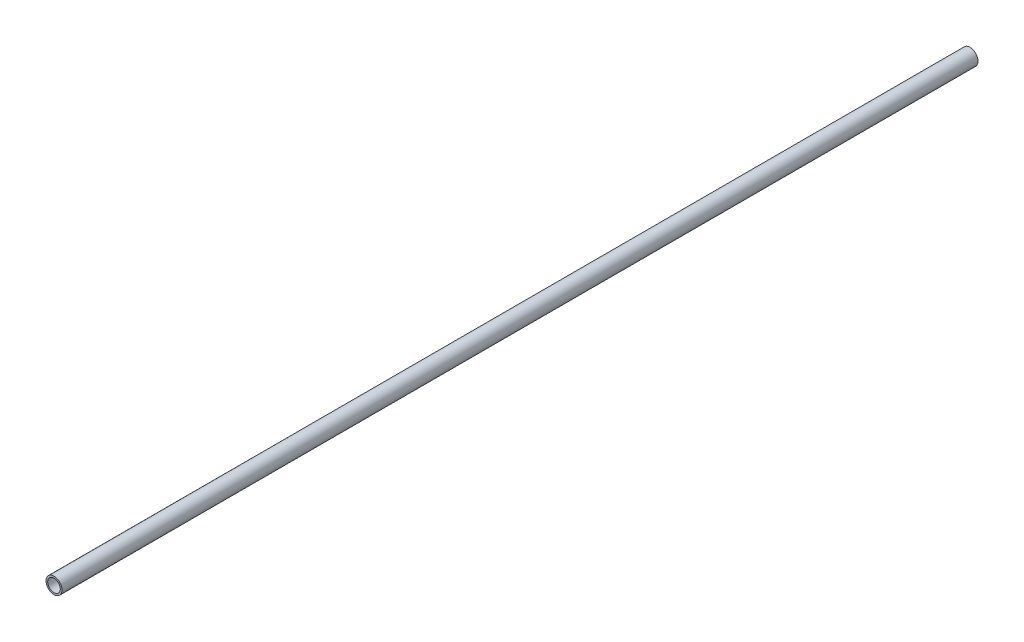
SolidWorks part; units mm, degrees
material "PVC 0.007 Plasticized"
ref_plane "Front Plane" through (0, 0, 0) normal (0, 0, 1) x (1, 0, 0)
ref_plane "Top Plane" through (0, 0, 0) normal (0, 1, 0) x (1, 0, 0)
ref_plane "Right Plane" through (0, 0, 0) normal (1, 0, 0) x (0, 0, -1)
sketch "Sketch1" plane through (0, 0, 0) normal (0, 0, 1) x (1, 0, 0)
  line L0 (10.4648, 0) -> (13.335, 0) construction
  circle A0 centre (0, 0) radius 13.335 construction
  circle A1 centre (0, 0) radius 10.4648 construction
  dimension "ID" = 20.9296
  dimension "OD" = 26.67
  dimension "Wall Thickness" = 2.8702
sketch "Sketch2" plane through (0, 0, 0) normal (1, 0, 0) x (0, 0, -1)
  line L0 (-762, 0) -> (762, 0) construction
  line L1 (-728.6625, 13.335) -> (-728.6625, -13.335) construction
  line L2 (728.6625, 13.335) -> (728.6625, -13.335) construction
  point P4 (0, 0)
  point P8 (-728.6625, 0)
  point P11 (728.6625, 0)
  dimension "Length" = 1524
  dimension "D1" = 33.3375
  dimension "D2" = 33.3375
  dimension "D3" = 26.67
sketch "Sketch3" plane through (0, 0, 0) normal (0, 0, 1) x (1, 0, 0)
  circle A0 centre (0, 0) radius 13.335
  circle A1 centre (0, 0) radius 13.335 construction
  circle A2 centre (0, 0) radius 10.4648 construction
  circle A3 centre (0, 0) radius 10.4648
extrude "Boss-Extrude1" add sketch "Sketch3" along normal up to vertex (762 mm away) and the other way up to vertex (762 mm away) up to point (0, 0, 762) other way up to point (0, 0, -762)
equation "\"D1@Sketch2\"=\"OD@Sketch1\" * 1.25"
equation "\"D2@Sketch2\"=\"D1@Sketch2\""
equation "\"D3@Sketch2\"= \"OD@Sketch1\""
